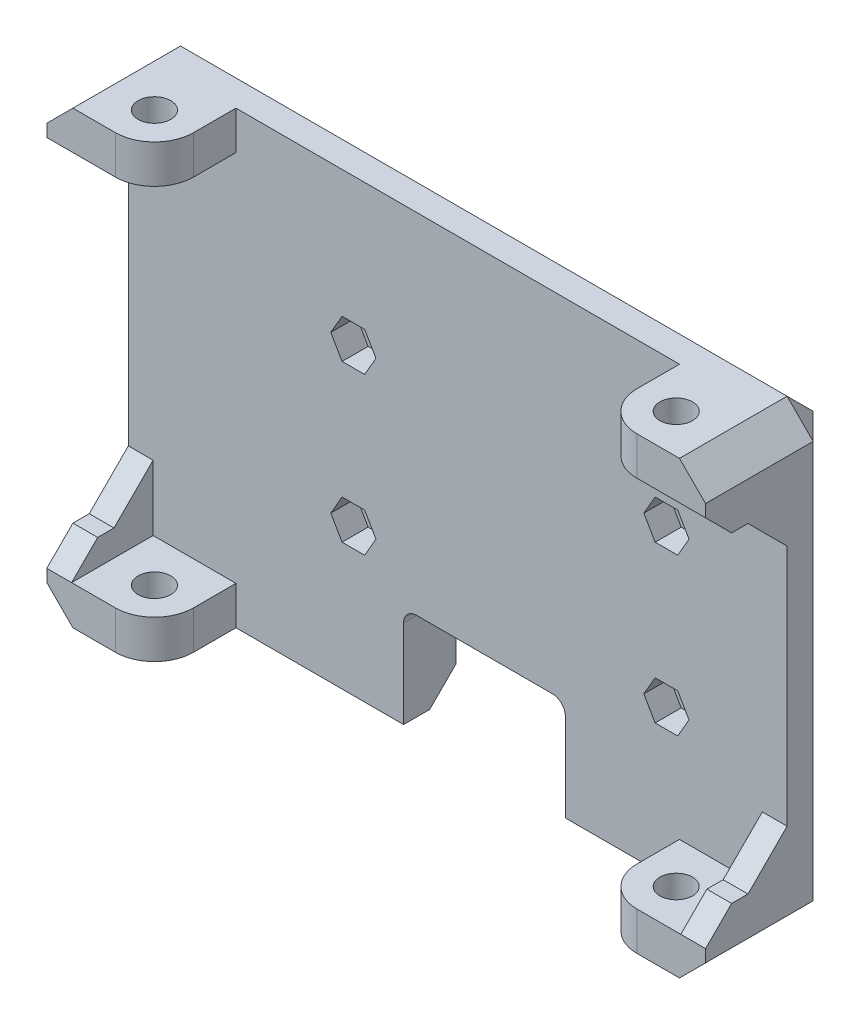
SolidWorks part; units mm, degrees
ref_plane "Front Plane" through (0, 0, 0) normal (0, 0, 1) x (1, 0, 0)
ref_plane "Top Plane" through (0, 0, 0) normal (0, 1, 0) x (1, 0, 0)
ref_plane "Right Plane" through (0, 0, 0) normal (1, 0, 0) x (0, 0, -1)
sketch "Sketch1" plane through (0, 0, 0) normal (0, 0, 1) x (1, 0, 0)
  line L1 (-23.25, 14.25) -> (23.25, 14.25) construction
  line L2 (-23.25, 14.25) -> (-23.25, -14.25) construction
  line L3 (-23.25, -14.25) -> (23.25, -14.25) construction
  line L4 (23.25, 14.25) -> (23.25, -14.25) construction
  line L5 (-23.25, 14.25) -> (23.25, -14.25) construction
  line L6 (-23.25, -14.25) -> (23.25, 14.25) construction
  line L7 (-23.25, 17.25) -> (23.25, 17.25)
  line L8 (-23.25, 17.25) -> (-23.25, -17.25)
  line L9 (-23.25, -17.25) -> (23.25, -17.25)
  line L10 (23.25, 17.25) -> (23.25, -17.25)
  point P0 (0, 0)
  dimension "D1" = 46.5
  dimension "D2" = 28.5
  dimension "D3" = 3
  dimension "D4" = 3
extrude "Boss-Extrude1" add sketch "Sketch1" along normal blind 4
sketch "Sketch2" plane through (0, 0, 4) normal (0, 0, 1) x (1, 0, 0)
  line L0 (23.25, -17.25) -> (23.25, 17.25) construction
  line L1 (-23.25, 17.25) -> (23.25, 17.25)
  line L2 (-23.25, 17.25) -> (-23.25, 14.3)
  line L3 (-23.25, 14.3) -> (23.25, 14.3)
  line L4 (23.25, 17.25) -> (23.25, 14.3)
  line L5 (-23.25, 17.25) -> (-23.25, -17.25) construction
  line L6 (23.25, -17.25) -> (-23.25, -17.25)
  line L7 (23.25, -17.25) -> (23.25, -14.3)
  line L8 (23.25, -14.3) -> (-23.25, -14.3)
  line L9 (-23.25, -17.25) -> (-23.25, -14.3)
  dimension "D1" = 2.95
  dimension "D2" = 2.95
extrude "Boss-Extrude2" add sketch "Sketch2" along normal blind 6.5
sketch "Sketch3" plane through (0, 17.25, 0) normal (0, 1, 0) x (1, 0, 0)
  line L0 (-23.25, -4) -> (23.25, -4) construction
  line L1 (23.25, -10.5) -> (23.25, 0) construction
  line L2 (-23.25, -10.5) -> (-23.25, 0) construction
  line L4 (23.25, -7.25) -> (20, -7.25) construction
  line L5 (-23.25, -7.25) -> (-20, -7.25) construction
  circle A0 centre (-20, -7.25) radius 1.25
  circle A1 centre (20, -7.25) radius 1.25
  dimension "D1" = 3.25
  dimension "D2" = 2.5
  dimension "D3" = 40
extrude "Cut-Extrude1" cut sketch "Sketch3" against normal through all
sketch "Sketch11" plane through (0, 17.25, 0) normal (0, 1, 0) x (1, 0, 0)
  line L0 (23.25, -10.5) -> (-23.25, -10.5) construction
  line L1 (-17, -7.25) -> (-17, -4)
  line L2 (-23.25, -4) -> (23.25, -4) construction
  line L3 (-17, -4) -> (17, -4)
  line L4 (17, -7.25) -> (17, -4)
  line L6 (23.25, -10.5) -> (-23.25, -10.5)
  line L10 (-23.25, -10.25) -> (-23.25, -10.5)
  line L12 (23.25, -10.5) -> (23.25, 0) construction
  line L13 (23.25, -10.25) -> (23.25, -10.5)
  line L14 (-20, -10.25) -> (-23.25, -10.25)
  line L15 (20, -10.25) -> (23.25, -10.25)
  arc A2 (-20, -10.25) -> (-17, -7.25) centre (-20, -7.25) ccw
  arc A3 (17, -7.25) -> (20, -10.25) centre (20, -7.25) ccw
  dimension "D1" = 6
extrude "Cut-Extrude8" cut sketch "Sketch11" against normal through all
sketch "Sketch5" plane through (0, 0, 0) normal (0, 0, -1) x (-1, 0, 0)
  line L0 (23.25, 17.25) -> (23.25, -17.25) construction
  line L1 (-16, 6) -> (8, 6) construction
  line L2 (-16, 6) -> (-16, -6) construction
  line L3 (-16, -6) -> (8, -6) construction
  line L4 (8, 6) -> (8, -6) construction
  line L6 (-23.25, 17.25) -> (23.25, 17.25) construction
  circle A0 centre (8, 6) radius 0.725
  circle A1 centre (8, -6) radius 0.725
  circle A2 centre (-16, -6) radius 0.725
  circle A3 centre (-16, 6) radius 0.725
  dimension "D1" = 1.45
  dimension "D4" = 15.25
  dimension "D5" = 11.25
  dimension "D2" = 12
  dimension "D3" = 24
extrude "Cut-Extrude3" cut sketch "Sketch5" against normal through all
sketch "Sketch21" plane through (0, 0, 0) normal (0, 0, -1) x (-1, 0, 0)
  line L0 (-23.25, -17.25) -> (-23.25, 17.25) construction
  line L1 (3.15, -16.7) -> (-7.25, -16.7) construction
  line L2 (3.15, -16.7) -> (3.15, -10.5) construction
  line L3 (3.15, -10.5) -> (-7.25, -10.5) construction
  line L4 (-7.25, -16.7) -> (-7.25, -10.5) construction
  line L5 (4.15, -17.7) -> (-8.25, -17.7)
  line L6 (-8.25, -17.7) -> (-8.25, -9.5)
  line L7 (4.15, -9.5) -> (-8.25, -9.5)
  line L8 (4.15, -17.7) -> (4.15, -9.5)
  dimension "D1" = 16
  dimension "D2" = 10.4
  dimension "D3" = 6.2
  dimension "D4" = 10.5
  dimension "D5" = 1
extrude "Cut-Extrude11" cut sketch "Sketch21" against normal through all
sketch "Sketch14" plane through (-23.25, 0, 0) normal (-1, 0, 0) x (0, 0, 1)
  line L8 (10.25, 17.25) -> (0, 17.25)
  line L9 (0, 17.25) -> (0, -17.25)
  line L10 (0, -17.25) -> (10.25, -17.25)
  line L11 (10.25, -17.25) -> (10.25, -14.3)
  line L12 (10.25, -14.3) -> (4, -14.3)
  line L13 (4, -14.3) -> (4, 14.3)
  line L14 (4, 14.3) -> (10.25, 14.3)
  line L15 (10.25, 14.3) -> (10.25, 17.25)
  line L16 (10.25, 17.25) -> (0, 17.25)
  line L18 (0, -17.25) -> (10.25, -17.25)
  line L19 (10.25, -17.25) -> (10.25, -14.3)
  line L20 (10.25, -14.3) -> (4, -14.3)
  line L21 (4, -14.3) -> (4, 14.3)
  line L22 (4, 14.3) -> (10.25, 14.3)
  line L23 (10.25, 14.3) -> (10.25, 17.25)
  line L24 (0, 17.25) -> (0, -17.25)
  dimension "D1" = 0
extrude "Boss-Extrude3" add sketch "Sketch14" along normal blind 0.1
sketch "Sketch15" plane through (23.25, 0, 0) normal (1, 0, 0) x (0, 0, -1)
  line L8 (-10.25, -17.25) -> (0, -17.25)
  line L9 (0, -17.25) -> (0, 17.25)
  line L10 (0, 17.25) -> (-10.25, 17.25)
  line L11 (-10.25, 17.25) -> (-10.25, 14.3)
  line L12 (-10.25, 14.3) -> (-4, 14.3)
  line L13 (-4, 14.3) -> (-4, -14.3)
  line L14 (-4, -14.3) -> (-10.25, -14.3)
  line L15 (-10.25, -14.3) -> (-10.25, -17.25)
  line L16 (-10.25, -17.25) -> (0, -17.25)
  line L18 (0, 17.25) -> (-10.25, 17.25)
  line L19 (-10.25, 17.25) -> (-10.25, 14.3)
  line L20 (-10.25, 14.3) -> (-4, 14.3)
  line L21 (-4, 14.3) -> (-4, -14.3)
  line L22 (-4, -14.3) -> (-10.25, -14.3)
  line L23 (-10.25, -14.3) -> (-10.25, -17.25)
  line L24 (0, -17.25) -> (0, 17.25)
  dimension "D1" = 0
extrude "Boss-Extrude4" add sketch "Sketch15" along normal blind 0.1
sketch "Sketch17" plane through (-23.35, 0, 0) normal (-1, 0, 0) x (0, 0, 1)
  line L9 (0, 17.25) -> (10.25, 17.25)
  line L10 (0, 17.25) -> (0, -17.25)
  line L11 (0, -17.25) -> (10.25, -17.25)
  line L12 (10.25, 17.25) -> (10.25, -17.25)
extrude "Boss-Extrude6" add sketch "Sketch17" along normal blind 1.9
sketch "Sketch18" plane through (23.35, 0, 0) normal (1, 0, 0) x (0, 0, -1)
  line L1 (0, 17.25) -> (-10.25, 17.25)
  line L2 (0, 17.25) -> (0, -17.25)
  line L3 (0, -17.25) -> (-10.25, -17.25)
  line L4 (-10.25, 17.25) -> (-10.25, -17.25)
extrude "Boss-Extrude7" add sketch "Sketch18" along normal blind 1.9
sketch "Sketch19" plane through (-25.25, 0, 0) normal (-1, 0, 0) x (0, 0, 1)
  line L0 (10.25, 12.3) -> (7, 12.3)
  line L1 (4, -14.3) -> (4, 14.3) construction
  line L2 (4, 9.3) -> (4, -9.3)
  line L3 (7, -12.3) -> (10.25, -12.3)
  line L4 (10.25, -12.3) -> (10.25, 12.3)
  line L5 (4, 14.3) -> (10.25, 14.3) construction
  line L6 (10.25, -14.3) -> (4, -14.3) construction
  line L7 (7, 12.3) -> (4, 9.3)
  line L8 (4, -9.3) -> (7, -12.3)
  point P1 (4, 12.3)
  point P6 (4, -12.3)
  dimension "D1" = 2
  dimension "D2" = 2
extrude "Cut-Extrude10" cut sketch "Sketch19" against normal through all
chamfer "Chamfer1" distance 2 angle 45 12 edges at (-24.3, -12.3, 10.25) (-24.3, 12.3, 10.25) (24.3, -12.3, 10.25) (24.3, 12.3, 10.25) (16.75, -17.25, 0) (-25.25, 0, 0) (0, 17.25, 0) (25.25, 0, 0) (25.25, 17.25, 5.125) (25.25, -17.25, 5.125) (-25.25, -17.25, 5.125) (-25.25, 17.25, 5.125)
fillet "Fillet2" radius 1 2 edges at (8.25, -9.5, 2) (-4.15, -9.5, 2)
sketch "Sketch22" plane through (0, 0, 4) normal (0, 0, 1) x (1, 0, 0)
  line L0 (7.25, -9.5) -> (-3.15, -9.5) construction
  line L1 (-7.134, 4.5) -> (-6.2679, 6)
  line L2 (-6.2679, 6) -> (-7.134, 7.5)
  line L3 (-7.134, 7.5) -> (-8.866, 7.5)
  line L4 (-8.866, 7.5) -> (-9.7321, 6)
  line L5 (-9.7321, 6) -> (-8.866, 4.5)
  line L6 (-8.866, 4.5) -> (-7.134, 4.5)
  line L7 (-7.134, -7.5) -> (-6.2679, -6)
  line L8 (-6.2679, -6) -> (-7.134, -4.5)
  line L9 (-7.134, -4.5) -> (-8.866, -4.5)
  line L10 (-8.866, -4.5) -> (-9.7321, -6)
  line L11 (-9.7321, -6) -> (-8.866, -7.5)
  line L12 (-8.866, -7.5) -> (-7.134, -7.5)
  line L13 (16.866, -7.5) -> (17.7321, -6)
  line L14 (17.7321, -6) -> (16.866, -4.5)
  line L15 (16.866, -4.5) -> (15.134, -4.5)
  line L16 (15.134, -4.5) -> (14.2679, -6)
  line L17 (14.2679, -6) -> (15.134, -7.5)
  line L18 (15.134, -7.5) -> (16.866, -7.5)
  line L19 (16.866, 4.5) -> (17.7321, 6)
  line L20 (17.7321, 6) -> (16.866, 7.5)
  line L21 (16.866, 7.5) -> (15.134, 7.5)
  line L22 (15.134, 7.5) -> (14.2679, 6)
  line L23 (14.2679, 6) -> (15.134, 4.5)
  line L24 (15.134, 4.5) -> (16.866, 4.5)
  circle A0 centre (-8, 6) radius 1.5 construction
  circle A1 centre (-8, -6) radius 1.5 construction
  circle A2 centre (16, -6) radius 1.5 construction
  circle A3 centre (16, 6) radius 1.5 construction
  dimension "D1" = 3
extrude "Cut-Extrude12" cut sketch "Sketch22" against normal blind 2
